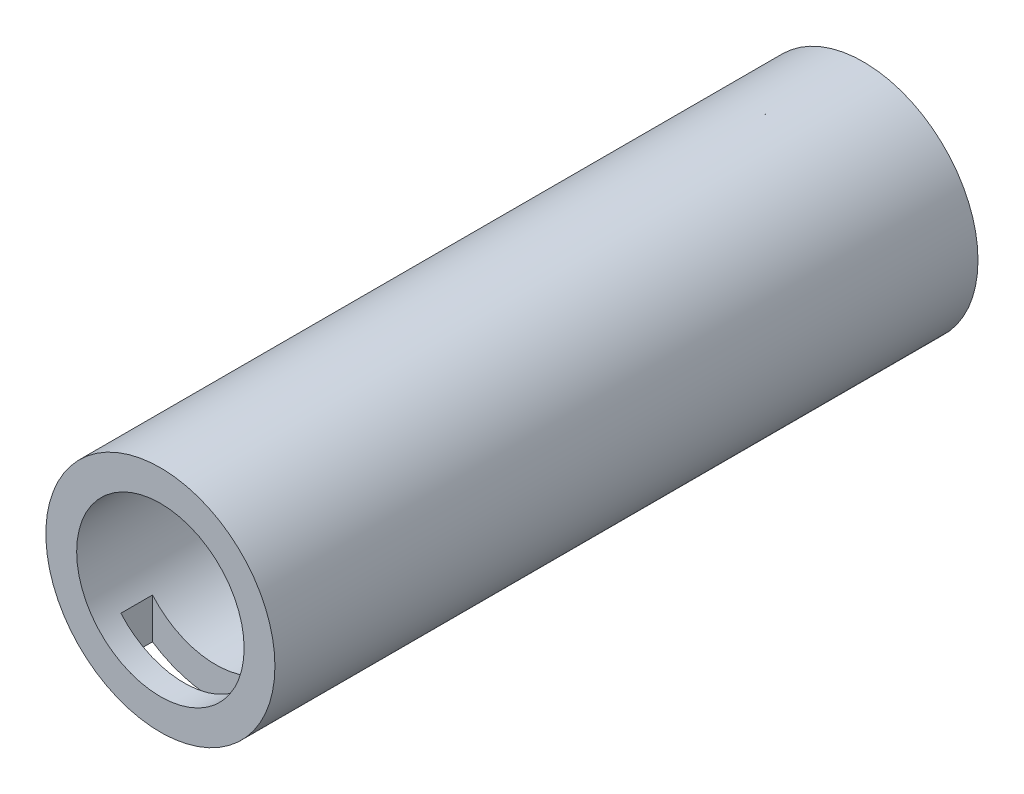
SolidWorks part; units mm, degrees
ref_plane "Front Plane" through (0, 0, 0) normal (0, 0, 1) x (1, 0, 0)
ref_plane "Top Plane" through (0, 0, 0) normal (0, 1, 0) x (1, 0, 0)
ref_plane "Right Plane" through (0, 0, 0) normal (1, 0, 0) x (0, 0, -1)
sketch "Sketch1" plane through (0, 0, 0) normal (0, 0, 1) x (1, 0, 0)
  circle A0 centre (0, 0) radius 18.415
  dimension "D1" = 36.83
extrude "Boss-Extrude2" add sketch "Sketch1" along normal blind 113.03
sketch "Sketch4" plane through (0, 0, 0) normal (0, 1, 0) x (1, 0, 0)
  line L1 (10.16, -109.22) -> (-10.16, -109.22)
  line L2 (10.16, -109.22) -> (10.16, -104.14)
  line L3 (10.16, -104.14) -> (-10.16, -104.14)
  line L4 (-10.16, -109.22) -> (-10.16, -104.14)
  dimension "D1" = 104.14
  dimension "D2" = 5.08
  dimension "D3" = 10.16
  dimension "D4" = 20.32
extrude "Cut-Extrude2" cut sketch "Sketch4" against normal blind 22.86 and the other way blind 12.7
sketch "Sketch5" plane through (0, 0, 0) normal (0, 0, -1) x (-1, 0, 0)
  circle A0 centre (0, 0) radius 13.462
  dimension "D1" = 26.924
extrude "Cut-Extrude3" cut sketch "Sketch5" against normal up to surface (107.95 mm away) from offset 5.08 up to face at (18.415, 0, 113.03)
